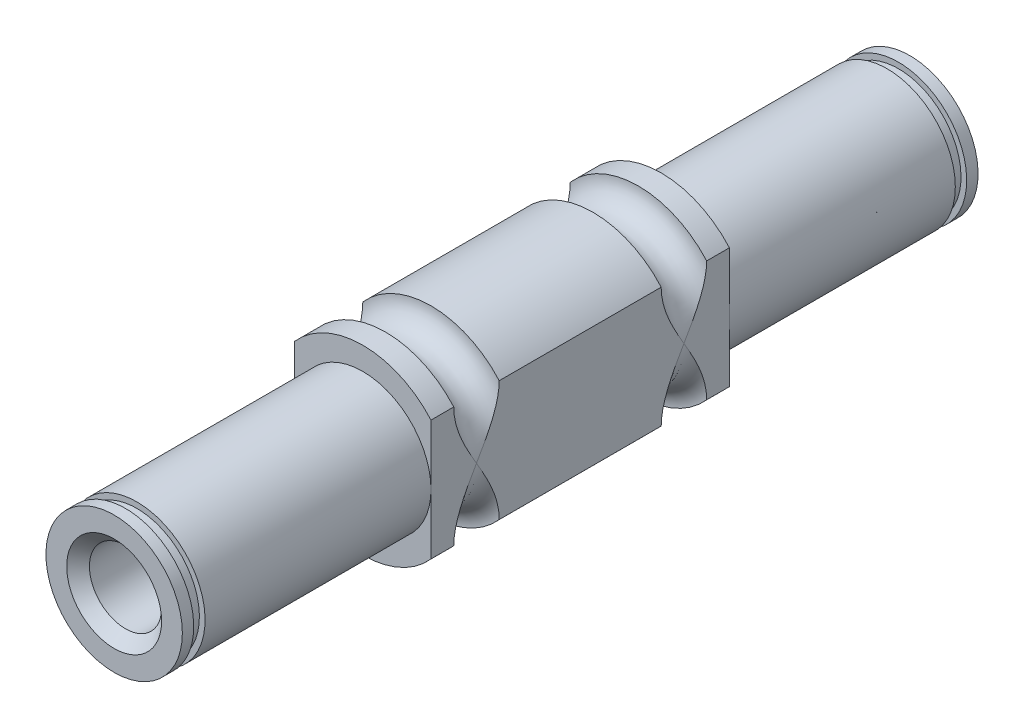
SolidWorks part; units mm, degrees
ref_plane "Front Plane" through (0, 0, 0) normal (0, 0, 1) x (1, 0, 0)
ref_plane "Top Plane" through (0, 0, 0) normal (0, 1, 0) x (1, 0, 0)
ref_plane "Right Plane" through (0, 0, 0) normal (1, 0, 0) x (0, 0, -1)
sketch "Sketch1" plane through (0, 0, 0) normal (0, 0, 1) x (1, 0, 0)
  circle A0 centre (0, 0) radius 8
  dimension "D1" = 16
extrude "Boss-Extrude1" add sketch "Sketch1" along normal blind 26.25
sketch "Sketch2" plane through (0, 0, 0) normal (0, 0, -1) x (-1, 0, 0)
  circle A0 centre (0, 0) radius 6
  dimension "D1" = 12
extrude "Boss-Extrude2" add sketch "Sketch2" along normal blind 21.875
sketch "Sketch3" plane through (0, 0, 26.25) normal (0, 0, 1) x (1, 0, 0)
  circle A0 centre (0, 0) radius 6
  dimension "D1" = 12
extrude "Boss-Extrude3" add sketch "Sketch3" along normal blind 21.875
sketch "Sketch5" plane through (0, 0, 0) normal (0, 0, -1) x (-1, 0, 0)
  line L0 (-6, 5.2915) -> (-6, -5.2915)
  line L1 (6, 5.2915) -> (6, -5.2915)
  circle A0 centre (0, 0) radius 8 construction
  circle A1 centre (0, 0) radius 8
  circle M4 centre (0, 0) radius 8
extrude "Cut-Extrude4" cut sketch "Sketch5" against normal through all both and the other way through all contours L0 M4 | L1 M4
sketch "Sketch6" plane through (6, 0, 0) normal (1, 0, 0) x (0, 0, -1)
  line L0 (-48.125, 0) -> (21.875, 0) construction
  line L11 (-48.125, 6) -> (-48.125, -6) construction
  line L12 (21.875, -6) -> (21.875, 6) construction
sketch "Sketch7" plane through (0, 0, 0) normal (1, 0, 0) x (0, 0, -1)
  line L1 (21.875, 6) -> (0, 6) construction
  line L2 (20.875, 6) -> (20.875, 5.5)
  line L3 (20.875, 5.5) -> (19.875, 5.5)
  line L4 (19.875, 5.5) -> (19.875, 6)
  line L5 (19.875, 6) -> (20.875, 6)
  line L6 (-48.125, 0) -> (21.875, 0) construction
  line L7 (-13.125, 5.2915) -> (-13.125, -5.2915) construction
  line L8 (-26.25, 5.2915) -> (0, 5.2915) construction
  line L9 (-26.25, -5.2915) -> (0, -5.2915) construction
  line L10 (-47.125, 6) -> (-47.125, 5.5)
  line L11 (-47.125, 5.5) -> (-46.125, 5.5)
  line L12 (-46.125, 6) -> (-47.125, 6)
  line L13 (-46.125, 5.5) -> (-46.125, 6)
  dimension "D2" = 1
revolve "Cut-Revolve1" cut sketch "Sketch7" angle 360 about L6
sketch "Sketch8" plane through (0, 0, 0) normal (1, 0, 0) x (0, 0, -1)
  line L0 (-48.125, 0) -> (21.875, 0) construction
  line L1 (-24.25, 8) -> (-20.25, 8)
  line L2 (-13.125, 8) -> (-13.125, -8) construction
  line L3 (-26.25, -8) -> (0, -8) construction
  line L4 (-6, 8) -> (-2, 8)
  arc A0 (-24.25, 8) -> (-20.25, 8) centre (-22.25, 8) ccw
  arc A1 (-2, 8) -> (-6, 8) centre (-4, 8) cw
  dimension "D2" = 4
revolve "Cut-Revolve2" cut sketch "Sketch8" angle 360 about L0
sketch "Sketch9" plane through (0, 0, 48.125) normal (0, 0, 1) x (1, 0, 0)
  circle A0 centre (0, 0) radius 3.175
  dimension "D1" = 6.35
extrude "Cut-Extrude5" cut sketch "Sketch9" against normal through all
chamfer "Chamfer1" distance 1 angle 45 2 edges at (3.175, 0, -21.875) (3.175, 0, 48.125)
equation "\"shaft\"= 12"
equation "\"brace\"= 16"
equation "\"shaft length\"= 70"
equation "\"D1@Sketch1\"=\"brace\""
equation "\"D1@Boss-Extrude1\"=\"shaft length\"*(3/8)"
equation "\"D1@Sketch2\"=\"shaft\""
equation "\"D1@Boss-Extrude2\"=\"shaft length\"*(5/16)"
equation "\"D1@Sketch3\"=\"shaft\""
equation "\"D1@Boss-Extrude3\"=\"shaft length\"*(5/16)"
equation "\"D2@Sketch8\"=\"brace\"-\"shaft\""
